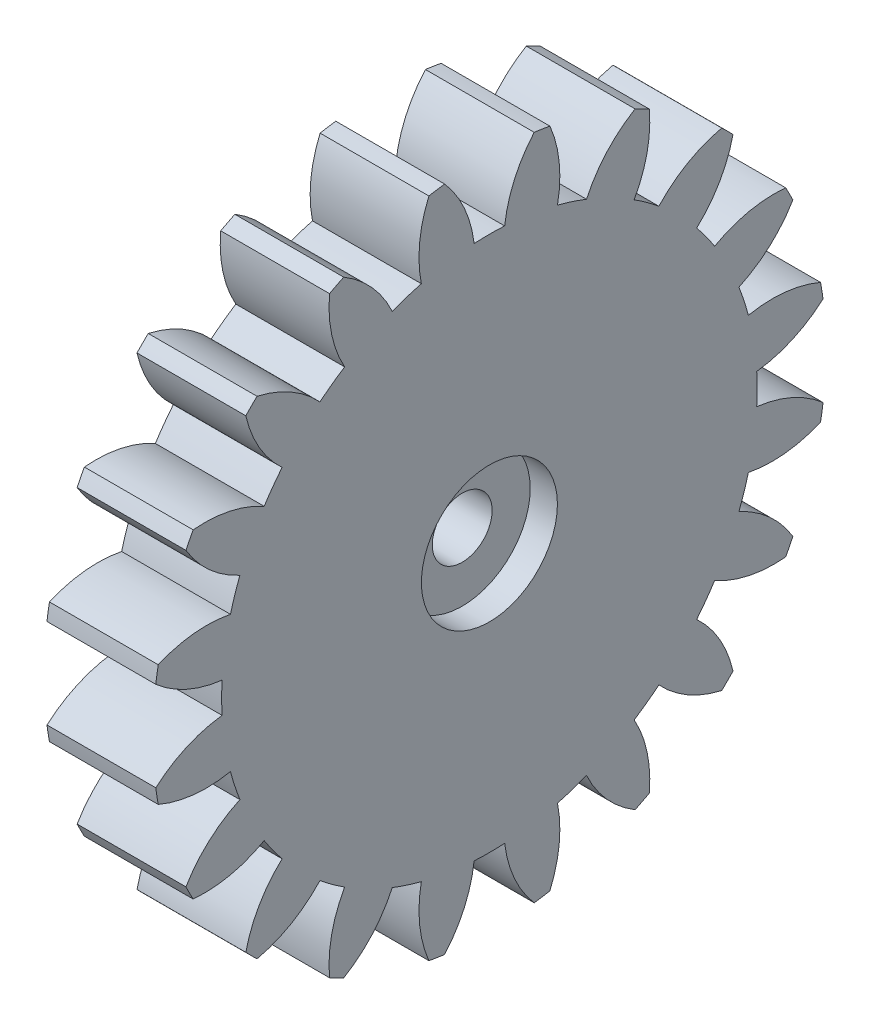
SolidWorks part; units mm, degrees
material "PLA"
ref_plane "Plane1" through (0, 0, 0) normal (0, 0, 1) x (1, 0, 0)
ref_plane "Plane2" through (0, 0, 0) normal (0, 1, 0) x (1, 0, 0)
ref_plane "Plane3" through (0, 0, 0) normal (1, 0, 0) x (0, 0, -1)
other "Configuration Table"
sketch "HoldingSke" plane through (0, 0, 0) normal (0, 1, 0) x (1, 0, 0)
  line L0 (0, 0) -> (0.8353, -0.304)
  line L1 (-15, 0) -> (100, 0) construction
  line L2 (0, 0) -> (-2.1039, 2.3779)
  line L3 (0, 0) -> (-11.863, 4.5341)
  line L4 (0, 0) -> (8.1152, 2.9537)
  line L5 (0, 0) -> (-46.8476, -17.4728)
  line L6 (0, 0) -> (-3.3159, -2.2372)
  line L7 (-2.1039, 2.3779) -> (8.6586, 51.2059)
  line L8 (-76.2, 54.61) -> (-75.7, 54.61)
  line L9 (-71.009, 38.7566) -> (-53.1078, 45.2721)
  line L10 (-76.2, 71.12) -> (104.1128, 71.12)
  line L11 (0, 0) -> (-4, 0)
  line L12 (-76.2, 101.6) -> (-76.158, 101.6)
  line L13 (24.9733, 27.94) -> (52.9518, 28.4284)
  line L14 (24.9733, 27.94) -> (24.9743, 27.94)
  line L15 (24.9733, 27.94) -> (100.4006, 29.5858)
  line L16 (-63.627, -1.125) -> (-12.827, -1.125)
  circle A0 centre (0, 0) radius 1.5
  circle A1 centre (0, 0) radius 9.8427
  circle A2 centre (0, 0) radius 37.5
  circle A3 centre (0, 0) radius 1.5
  dimension "MHD" = 19.6855
  dimension "Hub_dia" = 75
  dimension "Bore" = 3
  dimension "MBD" = 3
  dimension "Num_teeth" = 20
  dimension "Pitch" = 0.8889
  dimension "Overall_len" = 50
  dimension "Show_teeth" = 20
  dimension "Thickness" = 4
  dimension "OAL" = 50.0001
  dimension "T_dim" = 0.5
  dimension "Ap" = 20
  dimension "H" = 19.05
  dimension "Pitch_radius" = 180.3128
  dimension "Width" = 4
  dimension "Backlash" = 0.042
  dimension "Addendum_fac" = 1
  dimension "Dedendum_fac" = 1.25
  dimension "Clearance_fac" = 0.25
  dimension "Dedendum_add" = 0.001
  dimension "Module" = 1.125
sketch "BasProSke" plane through (0, 0, 0) normal (0, 1, 0) x (1, 0, 0)
  line L0 (-10, 0) -> (60, 0) construction
  line L1 (0, 0) -> (0, 12.375)
  line L2 (0, 0) -> (4, 0)
  line L3 (4, 0) -> (4, 12.375)
  line L4 (4, 12.375) -> (0, 12.375)
  dimension "Thickness" = 4
  dimension "Diameter" = 24.75
revolve "Base-Revolve" add sketch "BasProSke" angle 360 about L0
sketch "TooCutSke" plane through (0, 0, 0) normal (1, 0, 0) x (0, 0, -1)
  line L1 (0, 0) -> (0, 107) construction
  line L2 (0, 0) -> (-0.9561, 11.2093) construction
  line L3 (0, 0) -> (-3.5107, 22.1654) construction
  line L4 (-0.9561, 11.2093) -> (-1.7553, 11.0827) construction
  arc A0 (0.5613, 9.8267) -> (-0.5613, 9.8267) centre (0, 0) ccw
  arc A1 (1.6669, 12.2879) -> (-1.6669, 12.2879) centre (0, 0) ccw
  circle A2 centre (0, 0) radius 11.25 construction
  circle A3 centre (0, 0) radius 10.5715 construction
  arc A4 (-0.5613, 9.8267) -> (-1.6669, 12.2879) centre (-5.0301, 9.2981) ccw
  arc A5 (1.6669, 12.2879) -> (0.5613, 9.8267) centre (5.0301, 9.2981) ccw
  dimension "Root_dia" = 19.6855
  dimension "Overcut_dia" = 24.8008
  dimension "Pitch_dia" = 22.5
  dimension "Base_dia" = 21.1431
  dimension "Flank_rad" = 4.5
  dimension "Half_ang" = 9
  dimension "Half_CT" = 0.8092
extrude "ToothCut" cut sketch "TooCutSke" along normal through all
fillet "Breaks" [suppressed] radius 0.0225
fillet "RootFillets" [suppressed] radius 0.2823
pattern_circular "TeethCuts" count 20 over 360 about axis through (0, 0, 0) along (1, 0, 0) of "ToothCut", "RootFillets", "Breaks"
sketch "HubNeaOneSke" plane through (0, 0, 0) normal (-1, 0, 0) x (0, 0, 1)
  circle A0 centre (0, 0) radius 9.8427
  dimension "Diameter" = 19.6855
extrude "HubNearOne" [suppressed] add sketch "HubNeaOneSke" along normal blind 46.0001
sketch "HubNeaBotSke" plane through (0, 0, 0) normal (-1, 0, 0) x (0, 0, 1)
  circle A0 centre (0, 0) radius 9.8427
  dimension "Diameter" = 19.6855
extrude "HubNearBoth" [suppressed] add sketch "HubNeaBotSke" along normal blind 23
ref_plane "FarPln" through (4, 0, 0) normal (1, 0, 0) x (0, 0, -1)
sketch "HubFarSke" plane through (4, 0, 0) normal (1, 0, 0) x (0, 0, -1)
  circle A0 centre (0, 0) radius 9.8427
  dimension "Diameter" = 19.6855
extrude "HubFar" [suppressed] add sketch "HubFarSke" along normal blind 23
sketch "BorSke" plane through (0, 0, 0) normal (1, 0, 0) x (0, 0, -1)
  circle A0 centre (0, 0) radius 1.5
  dimension "Diameter" = 3
extrude "Bore" [suppressed] cut sketch "BorSke" along normal mid plane 100.0001
sketch "KeySke" plane through (0, 0, 0) normal (1, 0, 0) x (0, 0, -1)
  line L0 (-0.6, 0) -> (-0.6, 2)
  line L1 (-0.6, 2) -> (0.6, 2)
  line L2 (0.6, 2) -> (0.6, 0)
  line L3 (0, 0) -> (0, 34) construction
  line L4 (-0.6, 0) -> (0.6, 0)
  dimension "Offset" = 2
  dimension "Width" = 1.2
extrude "Keyway" [suppressed] cut sketch "KeySke" along normal mid plane 100.0001
pattern_circular "Keyway2" [suppressed] count 2 every 90 about axis through (-10, 0, 0) along (1, 0, 0)
hole_wizard "M2 Clearance Hole1" positions "Sketch1" profile "Sketch2" hole size "M2" standard "ANSI Metric" end condition up to next
sketch "Sketch1" plane through (4, 0, 0) normal (1, 0, 0) x (0, 0, -1)
  point P0 (0, 0)
sketch "Sketch2" plane through (4, 0, 0) normal (0, 1, 0) x (0, 0, -1)
  line L0 (0, 0) -> (0, 4)
  line L1 (0, 4) -> (1.1, 4)
  line L2 (1.1, 4) -> (1.1, 0)
  line L5 (1.1, 0) -> (0, 0)
  line L11 (0, -6.35) -> (0, 107.95) construction
  dimension "Thru Hole Dia." = 2.2
  dimension "Thru Hole Depth" = 4
sketch "Sketch3" plane through (4, 0, 0) normal (1, 0, 0) x (0, 0, -1)
  circle A0 centre (0, 0) radius 2.5
  dimension "D1" = 5
extrude "Cut-Extrude1" cut sketch "Sketch3" against normal blind 1
equation "' \"Module@HoldingSke\" = 6.35"
equation "' \"Num_teeth@HoldingSke\" = 12"
equation "' \"Ap@HoldingSke\" =  20"
equation "' \"Ap@HoldingSke\" = 20"
equation "' \"Width@HoldingSke\" = 0.5 * 25.4"
equation "' \"Hub_dia@HoldingSke\"= 1 * 25.4"
equation "' \"Hub_dia@HoldingSke\" = 1 * 25.4"
equation "' \"Overall_len@HoldingSke\" = 1.0 * 25.4"
equation "' \"Bore@HoldingSke\" = 0.75 * 25.4"
equation "' \"T_dim@HoldingSke\" = 0.1 * 25.4"
equation "' \"Width@KeySke\" = 0.25 * 25.4"
equation "' \"Show_teeth@HoldingSke\" = 13"
equation "' \"Backlash@HoldingSke\" = 0.009 * 25.4"
equation "' \"Addendum_fac@HoldingSke\" = 1.0"
equation "' \"Dedendum_fac@HoldingSke\" = 1.25"
equation "' \"Dedendum_add@HoldingSke\" = 0.00005 * 25.4"
equation "' \"Clearance_fac@HoldingSke\" = 0.25"
equation "\"Pitch@HoldingSke\" = 1 / \"Module@HoldingSke\""
equation "\"Overcut_dia@TooCutSke\" = (\"Num_teeth@HoldingSke\" + 2 * \"Addendum_fac@HoldingSke\") / \"Pitch@HoldingSke\" + 0.002 * 25.4"
equation "\"Pitch_dia@TooCutSke\" = \"Num_teeth@HoldingSke\" / \"Pitch@HoldingSke\""
equation "\"Base_dia@TooCutSke\" = \"Num_teeth@HoldingSke\" / \"Pitch@HoldingSke\" * cos((\"Ap@HoldingSke\"  * 3.14159265 / 180))"
equation "\"Root_dia@TooCutSke\" = (\"Num_teeth@HoldingSke\" + 2) / \"Pitch@HoldingSke\" - 2 * (\"Addendum_fac@HoldingSke\" + \"Dedendum_fac@HoldingSke\") / \"Pitch@HoldingSke\" - \"Dedendum_add@HoldingSke\" * 2"
equation "\"Half_ang@TooCutSke\" = 180 / \"Num_teeth@HoldingSke\""
equation "\"Half_CT@TooCutSke\" = \"Num_teeth@HoldingSke\" / \"Pitch@HoldingSke\" * sin((3.14159265 / 2 / \"Num_teeth@HoldingSke\")) / 2 - 7 * \"Backlash@HoldingSke\" / 4"
equation "\"Flank_rad@TooCutSke\" = \"Num_teeth@HoldingSke\" / \"Pitch@HoldingSke\" / 5"
equation "\"Radius@RootFillets\" = \"Clearance_fac@HoldingSke\" / \"Pitch@HoldingSke\" + \"Dedendum_add@HoldingSke\""
equation "\"Break_rad@Breaks\" = 0.02 / \"Pitch@HoldingSke\""
equation "\"Thickness@HoldingSke\" = \"Width@HoldingSke\""
equation "\"OAL@HoldingSke\" = \"Thickness@HoldingSke\""
equation "\"MHD@HoldingSke\" = (\"Num_teeth@HoldingSke\" + 2) / \"Pitch@HoldingSke\" - 2 * (\"Addendum_fac@HoldingSke\" + \"Dedendum_fac@HoldingSke\")  / \"Pitch@HoldingSke\" - \"Dedendum_add@HoldingSke\" * 2"
equation "\"MBD@HoldingSke\" = (\"Num_teeth@HoldingSke\" + 2) / \"Pitch@HoldingSke\" - 2 * (\"Addendum_fac@HoldingSke\" + \"Dedendum_fac@HoldingSke\")  / \"Pitch@HoldingSke\" - \"Dedendum_add@HoldingSke\" * 2 - 0.002 * 25.4"
equation "\"MHD@HoldingSke\" = ((sgn( \"MHD@HoldingSke\" - \"Hub_dia@HoldingSke\" )-1)*( \"MHD@HoldingSke\" - \"Hub_dia@HoldingSke\" ))/-2+ \"Hub_dia@HoldingSke\""
equation "\"MBD@HoldingSke\" = ((sgn( \"MBD@HoldingSke\" - \"Bore@HoldingSke\" )-1)*( \"MBD@HoldingSke\" - \"Bore@HoldingSke\" ))/-2+ \"Bore@HoldingSke\""
equation "\"OAL@HoldingSke\" = ((sgn( \"OAL@HoldingSke\" - \"Overall_len@HoldingSke\" )+1)*( \"OAL@HoldingSke\" - \"Overall_len@HoldingSke\" ))/2 + \"Overall_len@HoldingSke\" + 0.000002 * 25.4"
equation "\"Num_teeth@TeethCuts\" = int( \"Show_teeth@HoldingSke\" ) + 1"
equation "\"Num_teeth@TeethCuts\" = ((sgn( \"Num_teeth@TeethCuts\" - \"Num_teeth@HoldingSke\" )-1)*( \"Num_teeth@TeethCuts\" - \"Num_teeth@HoldingSke\" ))/-2+ \"Num_teeth@HoldingSke\""
equation "\"Num_teeth@TeethCuts\" = ((sgn( \"Num_teeth@TeethCuts\" - 2.0)+1)*( \"Num_teeth@TeethCuts\" - 2.0))/2 +2.0"
equation "\"Angle@TeethCuts\" = 360.0 / \"Num_teeth@HoldingSke\""
equation "\"Diameter@BasProSke\" = (\"Num_teeth@HoldingSke\" + 2 * \"Addendum_fac@HoldingSke\") / \"Pitch@HoldingSke\""
equation "\"Thickness@BasProSke\"  = \"Thickness@HoldingSke\""
equation "' \"Fillet_rad@BasProSke\" =  \"Thickness@HoldingSke\" * 0.05"
equation "' \"Fillet_rad@BasProSke\" = \"Thickness@HoldingSke\" * 0.05"
equation "\"MHD@HoldingSke\" = ((sgn( \"MHD@HoldingSke\" - \"Root_dia@TooCutSke\" )-1)*( \"MHD@HoldingSke\" - \"Root_dia@TooCutSke\" ))/-2+ \"Root_dia@TooCutSke\""
equation "\"Diameter@HubNeaOneSke\" = \"MHD@HoldingSke\""
equation "\"Length@HubNearOne\" = \"OAL@HoldingSke\" - \"Thickness@BasProSke\""
equation "\"Diameter@HubNeaBotSke\" = \"MHD@HoldingSke\""
equation "\"Length@HubNearBoth\" = ( \"OAL@HoldingSke\" - \"Thickness@BasProSke\" ) / 2.0"
equation "\"Thickness@FarPln\" = \"Thickness@BasProSke\""
equation "\"Diameter@HubFarSke\" = \"MHD@HoldingSke\""
equation "\"Length@HubFar\" = ( \"OAL@HoldingSke\" - \"Thickness@BasProSke\" ) / 2.0"
equation "\"Diameter@BorSke\" = \"MBD@HoldingSke\""
equation "\"D1@Bore\" = \"OAL@HoldingSke\" * 2.0"
equation "\"D1@Keyway\" = \"OAL@HoldingSke\" * 2.0"
equation "\"Offset@KeySke\" = \"T_dim@HoldingSke\" + \"MBD@HoldingSke\" / 2.0"
